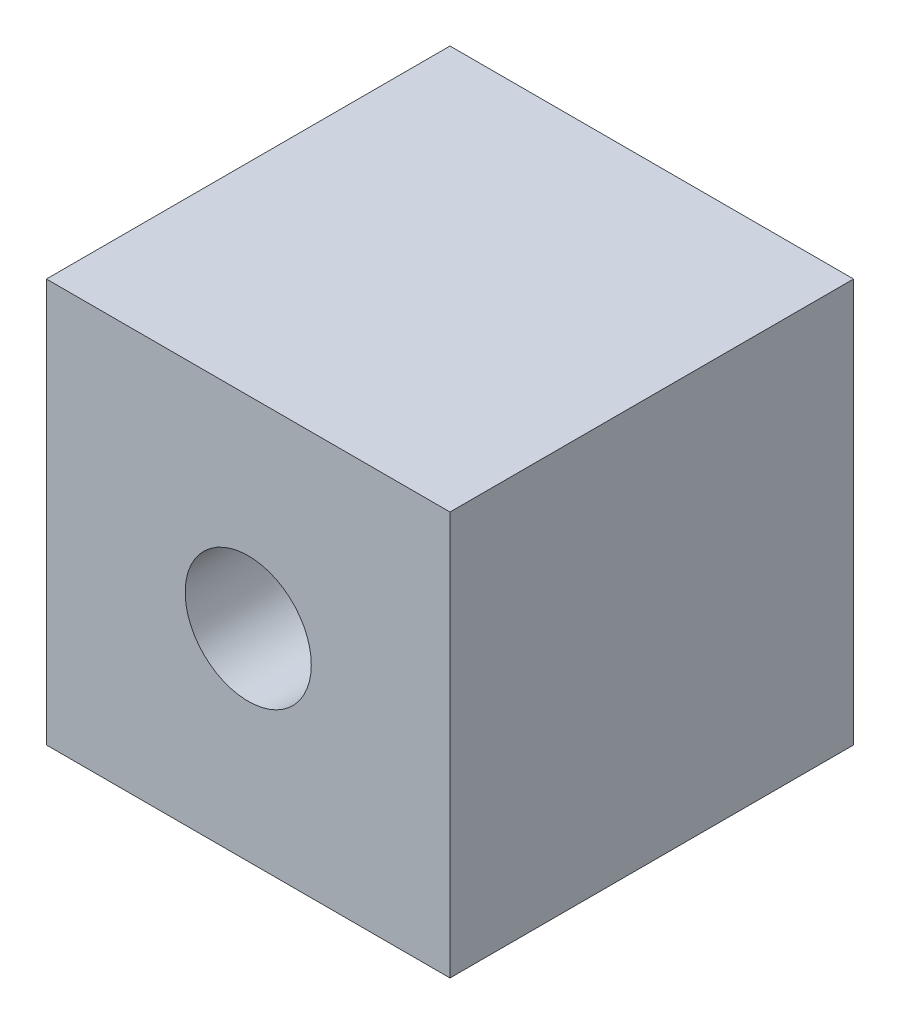
SolidWorks part; units mm, degrees
ref_plane "Front Plane" through (0, 0, 0) normal (0, 0, 1) x (1, 0, 0)
ref_plane "Top Plane" through (0, 0, 0) normal (0, 1, 0) x (1, 0, 0)
ref_plane "Right Plane" through (0, 0, 0) normal (1, 0, 0) x (0, 0, -1)
sketch "Sketch1" plane through (0, 0, 0) normal (0, 1, 0) x (1, 0, 0)
  line L1 (-24, -24) -> (24, -24)
  line L2 (-24, -24) -> (-24, 24)
  line L3 (-24, 24) -> (24, 24)
  line L4 (24, -24) -> (24, 24)
  line L5 (-24, -24) -> (24, 24) construction
  line L6 (-24, 24) -> (24, -24) construction
  point P0 (0, 0)
  dimension "D1" = 48
  dimension "D2" = 48
extrude "Boss-Extrude1" add sketch "Sketch1" along normal blind 48
sketch "Sketch2" plane through (0, 0, 24) normal (0, 0, 1) x (1, 0, 0)
  line L0 (-24, 48) -> (-24, 0) construction
  line L2 (-24, 0) -> (24, 0) construction
  circle A0 centre (0, 24) radius 7.5
  dimension "D1" = 15
  dimension "D2" = 24
  dimension "D3" = 24
extrude "Cut-Extrude1" cut sketch "Sketch2" against normal through all
